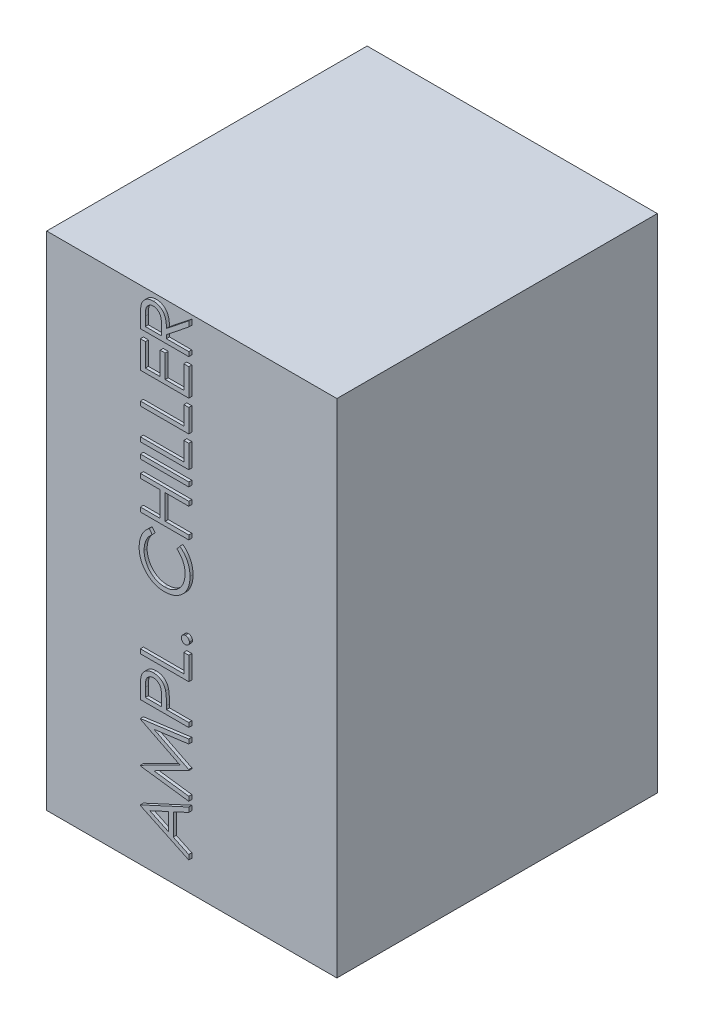
SolidWorks part; units mm, degrees
ref_plane "Front Plane" through (0, 0, 0) normal (0, 0, 1) x (1, 0, 0)
ref_plane "Top Plane" through (0, 0, 0) normal (0, 1, 0) x (1, 0, 0)
ref_plane "Right Plane" through (0, 0, 0) normal (1, 0, 0) x (0, 0, -1)
sketch "Sketch1" plane through (0, 0, 0) normal (0, 0, 1) x (1, 0, 0)
  line L1 (0, 0) -> (-480, 0)
  line L2 (0, 0) -> (0, -830)
  line L3 (0, -830) -> (-480, -830)
  line L4 (-480, 0) -> (-480, -830)
  dimension "D1" = 480
  dimension "D2" = 830
extrude "Boss-Extrude1" add sketch "Sketch1" along normal blind 530
sketch "Sketch2" plane through (0, 0, 530) normal (0, 0, 1) x (1, 0, 0)
  line L0 (-240, 0) -> (-240, -830) construction
  line L1 (0, 0) -> (-480, 0) construction
  line L2 (-480, -830) -> (0, -830) construction
  text T0 " AMPL. CHILLER" font "Century Gothic" height 80
extrude "Boss-Extrude2" add sketch "Sketch2" along normal blind 5
